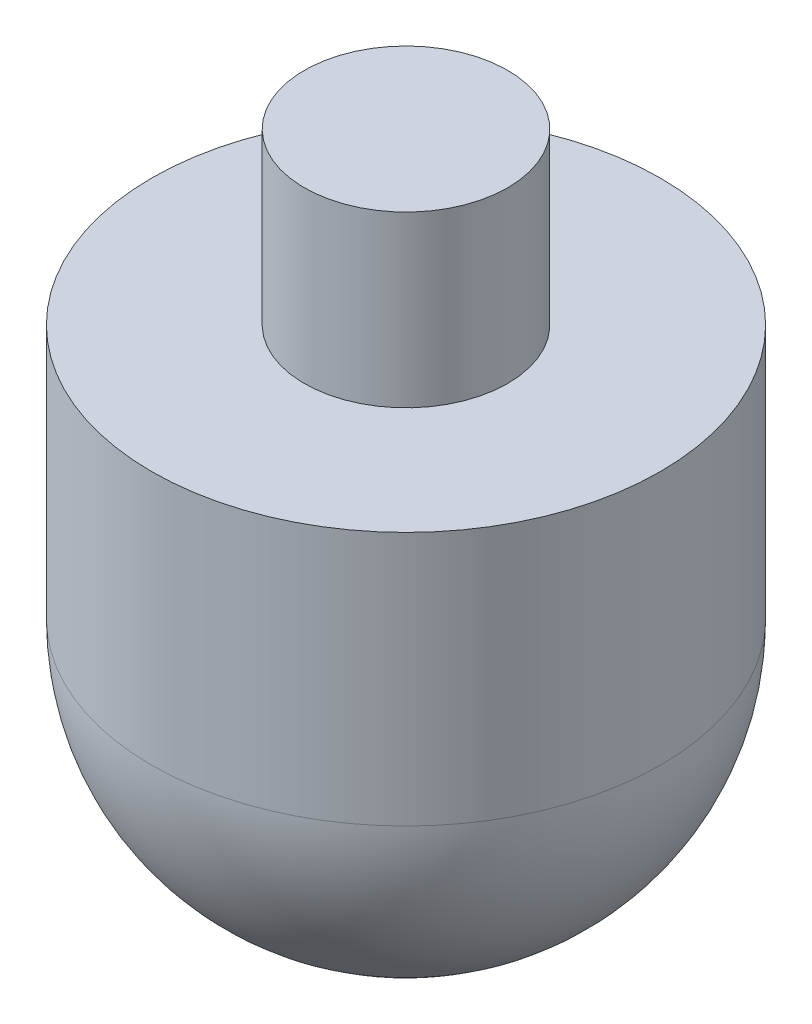
SolidWorks part; units mm, degrees
ref_plane "Front Plane" through (0, 0, 0) normal (0, 0, 1) x (1, 0, 0)
ref_plane "Top Plane" through (0, 0, 0) normal (0, 1, 0) x (1, 0, 0)
ref_plane "Right Plane" through (0, 0, 0) normal (1, 0, 0) x (0, 0, -1)
sketch "Sketch1" plane through (0, 0, 0) normal (0, 0, 1) x (1, 0, 0)
  line L0 (0, -24.3653) -> (0, 30.6426) construction
  line L1 (0, -15) -> (0, 25)
  line L3 (15, 0) -> (15, 15)
  line L4 (15, 15) -> (6, 15)
  line L5 (6, 15) -> (6, 25)
  line L6 (6, 25) -> (0, 25)
  arc A0 (0, -15) -> (15, 0) centre (0, 0) ccw
  dimension "D1" = 15
  dimension "D2" = 25
  dimension "D3" = 10
  dimension "D4" = 12
  dimension "D5" = 30
revolve "Revolve1" add sketch "Sketch1" angle 360 about L0
